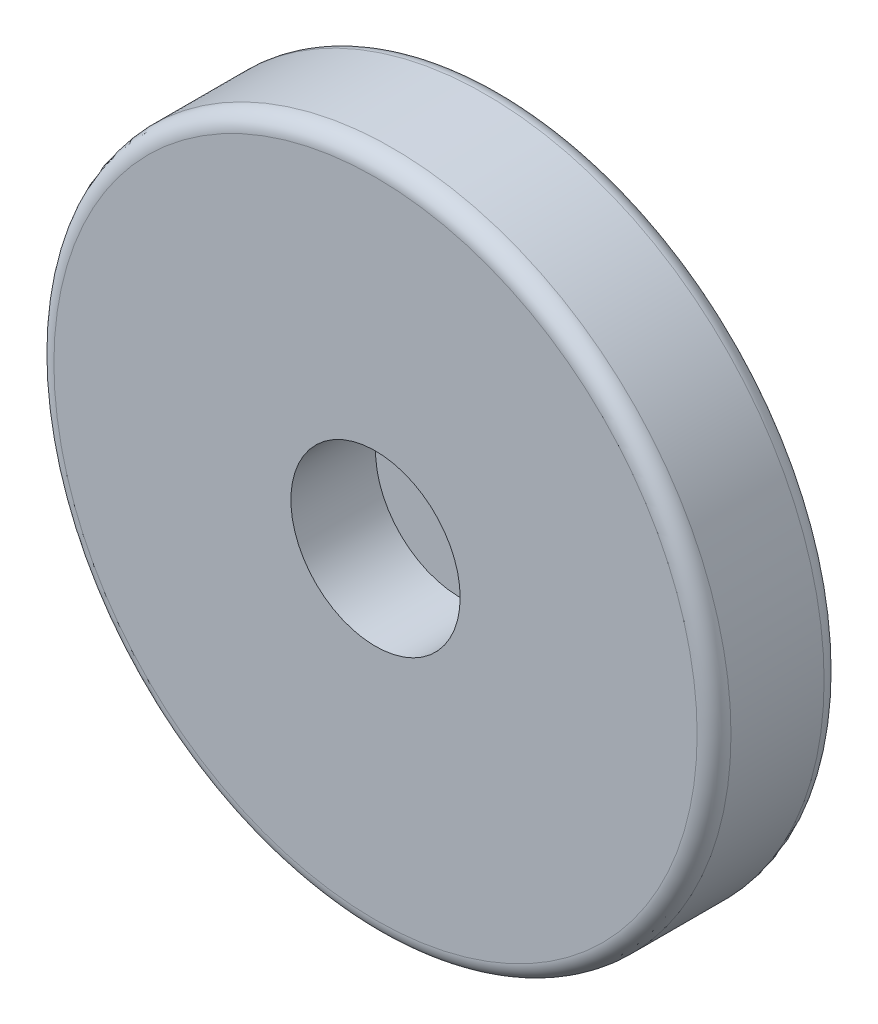
SolidWorks part; units mm, degrees
ref_plane "Front Plane" through (0, 0, 0) normal (0, 0, 1) x (1, 0, 0)
ref_plane "Top Plane" through (0, 0, 0) normal (0, 1, 0) x (1, 0, 0)
ref_plane "Right Plane" through (0, 0, 0) normal (1, 0, 0) x (0, 0, -1)
sketch "Sketch1" plane through (0, 0, 0) normal (0, 0, 1) x (1, 0, 0)
  circle A0 centre (0, 0) radius 101.6
  dimension "D1" = 203.2
extrude "Wheel" add sketch "Sketch1" along normal mid plane 38.1
fillet "Fillet1" radius 5.08 2 edges at (101.6, 0, -19.05) (101.6, 0, 19.05)
sketch "Sketch2" plane through (0, 0, 19.05) normal (0, 0, 1) x (1, 0, 0)
  circle A0 centre (0, 0) radius 25.4
sketch "Sketch4" plane through (0, 0, -19.05) normal (0, 0, -1) x (-1, 0, 0)
  line L0 (0, 0) -> (0, 96.52) construction
  circle A0 centre (0, 0) radius 96.52 construction
extrude "Cut-Extrude1" cut sketch "Sketch2" against normal blind 25.4 contours A0
